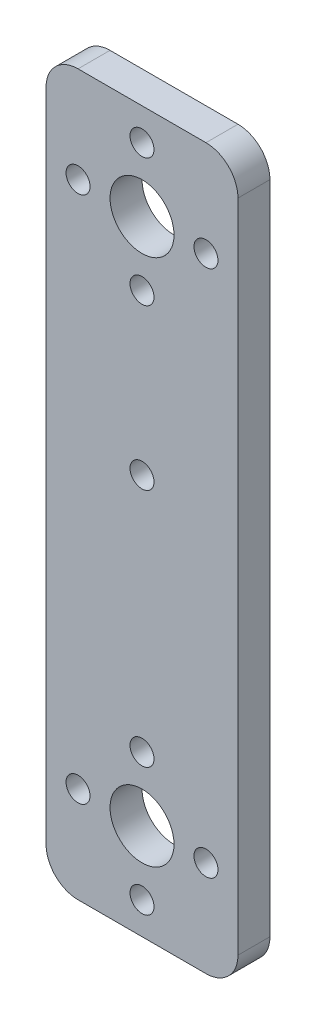
SolidWorks part; units mm, degrees
material "Acrylic (Medium-high impact)"
ref_plane "Front Plane" through (0, 0, 0) normal (0, 0, 1) x (1, 0, 0)
ref_plane "Top Plane" through (0, 0, 0) normal (0, 1, 0) x (1, 0, 0)
ref_plane "Right Plane" through (0, 0, 0) normal (1, 0, 0) x (0, 0, -1)
sketch "Sketch1" plane through (0, 0, 0) normal (0, 0, 1) x (1, 0, 0)
  line L1 (-57.2967, 34.9503) -> (-33.2967, 34.9503)
  line L2 (-57.2967, 34.9503) -> (-57.2967, -55.0497)
  line L3 (-57.2967, -55.0497) -> (-33.2967, -55.0497)
  line L4 (-33.2967, 34.9503) -> (-33.2967, -55.0497)
  dimension "D1" = 90
  dimension "D2" = 24
extrude "Boss-Extrude1" add sketch "Sketch1" along normal blind 4 contours L2 L3 L4 L1
sketch "Sketch2" plane through (0, 0, 4) normal (0, 0, 1) x (1, 0, 0)
  circle A0 centre (-45.2967, -43.0497) radius 4
  circle A1 centre (-37.2967, -43.0497) radius 1.5
  circle A2 centre (-45.2967, -51.0497) radius 1.5
  circle A3 centre (-45.2967, -43.0497) radius 4
  circle A4 centre (-53.2967, -43.0497) radius 1.5
  circle A5 centre (-45.2967, -43.0497) radius 4
  circle A6 centre (-45.2967, -35.0497) radius 1.5
  circle A7 centre (-45.2967, -43.0497) radius 4
  circle A18 centre (-45.2967, 30.9503) radius 1.5
  circle A19 centre (-37.2967, 22.9503) radius 1.5
  circle A20 centre (-45.2967, 14.9503) radius 1.5
  circle A21 centre (-53.2967, 22.9503) radius 1.5
  circle A22 centre (-45.2967, 22.9503) radius 4
  point P21 (-45.2967, -17.0497)
  dimension "D1" = 66
  dimension "D2" = 8
  dimension "D3" = 8
  dimension "D4" = 8
  dimension "D5" = 8
extrude "Cut-Extrude1" cut sketch "Sketch2" against normal blind 4 contours A6 | A0 | A1 | A2 | A4 | A21 | A18 | A22 | A19 | A20
fillet "Fillet1" radius 4 4 edges at (-57.2967, -55.0497, 2) (-33.2967, -55.0497, 2) (-57.2967, 34.9503, 2) (-33.2967, 34.9503, 2)
sketch "Sketch3" plane through (0, 0, 4) normal (0, 0, 1) x (1, 0, 0)
  circle A0 centre (-45.2967, -5.0497) radius 1.5
  circle A1 centre (-45.2967, 22.9503) radius 4 construction
  dimension "D1" = 28
extrude "Cut-Extrude2" cut sketch "Sketch3" against normal blind 4 contours A0
